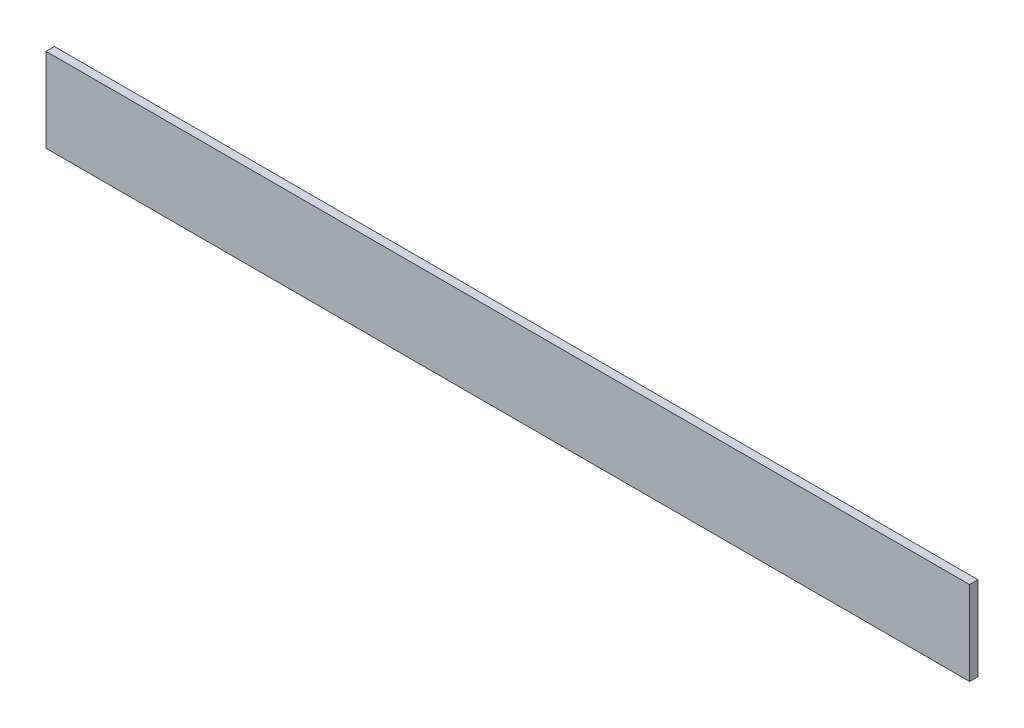
SolidWorks part; units mm, degrees
ref_plane "Front Plane" through (0, 0, 0) normal (0, 0, 1) x (1, 0, 0)
ref_plane "Top Plane" through (0, 0, 0) normal (0, 1, 0) x (1, 0, 0)
ref_plane "Right Plane" through (0, 0, 0) normal (1, 0, 0) x (0, 0, -1)
sketch "Sketch1" plane through (0, 0, 0) normal (0, 0, 1) x (1, 0, 0)
  line L1 (-275, 25) -> (275, 25)
  line L2 (-275, 25) -> (-275, -25)
  line L3 (-275, -25) -> (275, -25)
  line L4 (275, 25) -> (275, -25)
  line L5 (-275, 25) -> (275, -25) construction
  line L6 (-275, -25) -> (275, 25) construction
  point P0 (0, 0)
  dimension "D1" = 550
  dimension "D2" = 50
extrude "Boss-Extrude1" add sketch "Sketch1" along normal blind 5
